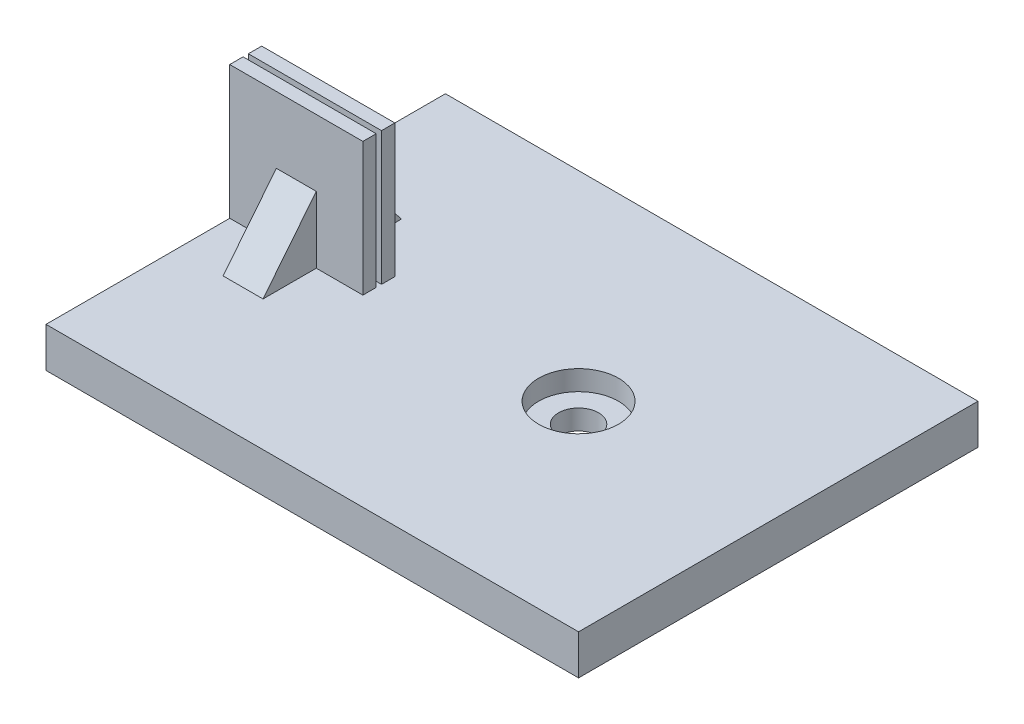
SolidWorks part; units mm, degrees
ref_plane "Front Plane" through (0, 0, 0) normal (0, 0, 1) x (1, 0, 0)
ref_plane "Top Plane" through (0, 0, 0) normal (0, 1, 0) x (1, 0, 0)
ref_plane "Right Plane" through (0, 0, 0) normal (1, 0, 0) x (0, 0, -1)
sketch "Sketch1" plane through (0, 0, 0) normal (0, 1, 0) x (1, 0, 0)
  line L0 (-25, 0) -> (15, 0) construction
  line L1 (-25, 15) -> (15, 15)
  line L2 (-25, 15) -> (-25, -15)
  line L3 (-25, -15) -> (15, -15)
  line L4 (15, 15) -> (15, -15)
  dimension "D1" = 40
  dimension "D2" = 30
  dimension "D3" = 15
extrude "Boss-Extrude1" add sketch "Sketch1" along normal blind 3
sketch "Sketch2" plane through (0, 3, 0) normal (0, 1, 0) x (1, 0, 0)
  circle A0 centre (0, 0) radius 3
  dimension "D1" = 6
extrude "Cut-Extrude1" cut sketch "Sketch2" against normal blind 1.5
sketch "Sketch3" plane through (0, 1.5, 0) normal (0, 1, 0) x (1, 0, 0)
  circle A0 centre (0, 0) radius 1.5
  dimension "D1" = 3
extrude "Cut-Extrude2" cut sketch "Sketch3" against normal through all
sketch "Sketch4" plane through (0, 0, 0) normal (0, -1, 0) x (1, 0, 0)
  circle A0 centre (0, 0) radius 3
  circle A1 centre (0, 0) radius 5
  dimension "D1" = 6
  dimension "D2" = 10
extrude "Cut-Extrude3" cut sketch "Sketch4" against normal blind 0.5
sketch "Sketch6" plane through (0, 3, 0) normal (0, 1, 0) x (1, 0, 0)
  line L0 (0, 0) -> (-25, 0) construction
  line L1 (-25, -1.2) -> (-15, -1.2)
  line L2 (-25, -1.2) -> (-25, -0.2)
  line L3 (-25, -0.2) -> (-15, -0.2)
  line L4 (-15, -1.2) -> (-15, -0.2)
  line L5 (-25, 0.2) -> (-15, 0.2)
  line L6 (-25, 0.2) -> (-25, 1.2)
  line L7 (-25, 1.2) -> (-15, 1.2)
  line L8 (-15, 0.2) -> (-15, 1.2)
  line L9 (-25, 15) -> (-25, -15) construction
  line L10 (-25, 1.2) -> (-25, -1.2) construction
  point P14 (0, 0)
  point P15 (-25, 0)
  dimension "D1" = 10
  dimension "D2" = 1
  dimension "D3" = 0.2
extrude "Boss-Extrude2" add sketch "Sketch6" along normal blind 10
ref_plane "Plane1" through (-20, 0, 0) normal (1, 0, 0) x (0, 0, -1)
sketch "Sketch10" plane through (-20, 0, 0) normal (1, 0, 0) x (0, 0, -1)
  line L0 (-1.2, 8) -> (-5.2, 3)
  line L1 (-1.2, 13) -> (-1.2, 3) construction
  line L2 (-15, 3) -> (15, 3) construction
  point P6 (-1.2, 8)
  point P7 (-5.9968, 3)
  point P9 (-1.2, 7.8583)
  dimension "D1" = 4
rib "Rib5" sketch "Sketch10" sketch "Sketch10" thickness 3 extrusion direction parallel to sketch draft on no parameters "D1"=3
mirror "Mirror1" about plane through (0, 0, 0) normal (0, 0, 1) of "Rib5"
